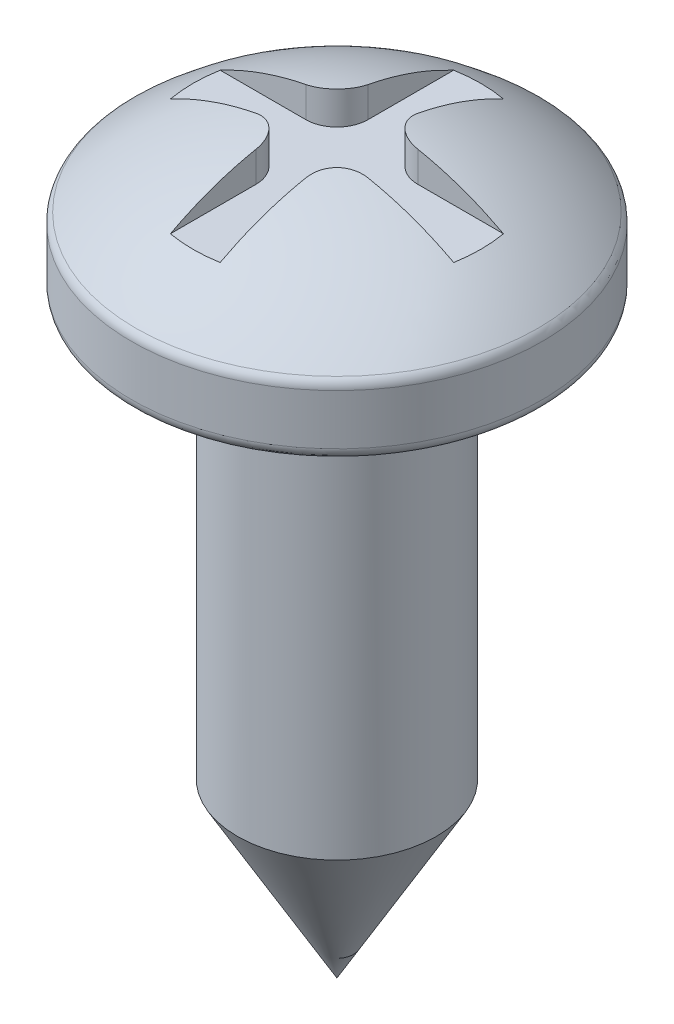
SolidWorks part; units mm, degrees
material "acero"
ref_plane "Alzado" through (0, 0, 0) normal (0, 0, 1) x (1, 0, 0)
ref_plane "Planta" through (0, 0, 0) normal (0, 1, 0) x (1, 0, 0)
ref_plane "Vista lateral" through (0, 0, 0) normal (1, 0, 0) x (0, 0, -1)
sketch "Croquis1" plane through (0, 0, 0) normal (0, 0, 1) x (1, 0, 0)
  line L0 (0, 0) -> (0, 11.9) construction
  line L1 (0, 0) -> (0, 11.9)
  line L2 (3.3, 9.7) -> (3.3, 10.5104)
  line L3 (3.1, 9.5) -> (1.6, 9.5)
  line L4 (1.6, 9.5) -> (1.6, 2.7713)
  line L5 (1.6, 2.7713) -> (0, 0)
  arc A0 (3.1, 9.5) -> (3.3, 9.7) centre (3.1, 9.7) ccw
  arc A1 (3.2318, 10.6609) -> (0, 11.9) centre (-0.0635, 6.9004) ccw
  arc A2 (3.3, 10.5104) -> (3.2318, 10.6609) centre (3.1, 10.5104) ccw
  point P11 (3.3, 9.5)
  point P14 (3.3, 10.6)
  dimension "D7" = 0.2
  dimension "D8" = 5
  dimension "D1" = 11.9
  dimension "D2" = 30
  dimension "D3" = 1.1
  dimension "D4" = 1.6
  dimension "D5" = 3.3
  dimension "D9" = 9.5
revolve "Revolución1" add sketch "Croquis1" angle 360 about L0
sketch "Croquis2" plane through (0, 9.5, 0) normal (0, -1, 0) x (1, 0, 0)
  line L0 (0, 0) -> (0, 3.3) construction
  line L1 (-0.4, 3.2) -> (-0.4, 0.9)
  line L2 (-0.9, 0.4) -> (-3.2, 0.4)
  line L3 (-3.2, 0.4) -> (-3.2, -0.4)
  line L4 (-3.2, -0.4) -> (-0.9, -0.4)
  line L5 (-0.4, -0.9) -> (-0.4, -3.2)
  line L6 (-0.4, -3.2) -> (0.4, -3.2)
  line L7 (0.4, -3.2) -> (0.4, -0.9)
  line L8 (0.9, -0.4) -> (3.2, -0.4)
  line L9 (3.2, -0.4) -> (3.2, 0.4)
  line L10 (3.2, 0.4) -> (0.9, 0.4)
  line L11 (0.4, 0.9) -> (0.4, 3.2)
  line L12 (0.4, 3.2) -> (-0.4, 3.2)
  circle A0 centre (0, 0) radius 3.3 construction
  arc A1 (-0.4, -0.9) -> (-0.9, -0.4) centre (-0.9, -0.9) ccw
  arc A2 (0.4, -0.9) -> (0.9, -0.4) centre (0.9, -0.9) cw
  arc A3 (0.9, 0.4) -> (0.4, 0.9) centre (0.9, 0.9) cw
  arc A4 (-0.9, 0.4) -> (-0.4, 0.9) centre (-0.9, 0.9) ccw
  point P26 (-0.4, 0.4)
  dimension "D12" = 0.5
  dimension "D1" = 0.4
  dimension "D2" = 0.8
  dimension "D3" = 3.2
  dimension "D4" = 3.2
  dimension "D5" = 3.2
  dimension "D6" = 3.2
  dimension "D7" = 0.4
  dimension "D8" = 0.4
  dimension "D9" = 0.4
  dimension "D10" = 0.4
  dimension "D11" = 0.4
extrude "Cortar-Extruir1" cut sketch "Croquis2" against normal blind 3 from offset 1.8
